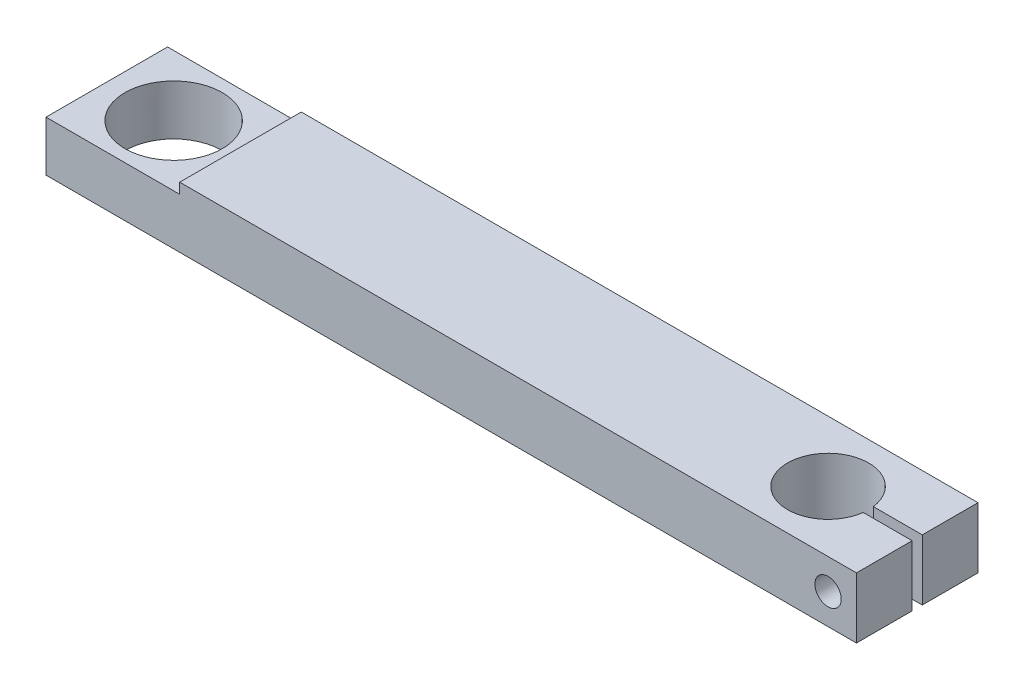
SolidWorks part; units mm, degrees
material "1060 Alloy"
ref_plane "Front Plane" through (0, 0, 0) normal (0, 0, 1) x (1, 0, 0)
ref_plane "Top Plane" through (0, 0, 0) normal (0, 1, 0) x (1, 0, 0)
ref_plane "Right Plane" through (0, 0, 0) normal (1, 0, 0) x (0, 0, -1)
sketch "Sketch1" plane through (0, 0, 0) normal (0, 1, 0) x (1, 0, 0)
  line L0 (87.9216, 1.25) -> (100, 1.25)
  line L1 (-100, 15) -> (100, 15)
  line L2 (-100, 15) -> (-100, -15)
  line L3 (-100, -15) -> (100, -15)
  line L4 (100, 15) -> (100, -15)
  line L5 (-100, 15) -> (100, -15) construction
  line L6 (-100, -15) -> (100, 15) construction
  line L7 (100, 1.25) -> (100, 0)
  line L8 (100, 0) -> (100, -1.25)
  line L9 (100, -1.25) -> (87.9216, -1.25)
  line L10 (78, 0) -> (119.9391, 0) construction
  circle A0 centre (-83.5, 0) radius 12
  circle A1 centre (78, 0) radius 10
  point P0 (0, 0)
  dimension "D3" = 24
  dimension "D4" = 20
  dimension "D1" = 200
  dimension "D2" = 30
  dimension "D5" = 16.5
  dimension "D6" = 161.5
  dimension "D7" = 2.5
  dimension "D8" = 1.25
extrude "Boss-Extrude1" add sketch "Sketch1" along normal blind 15 contours A1 L0 L4 L1 L2 L3 L9 A0
sketch "Sketch2" plane through (0, 0, -15) normal (0, 0, -1) x (-1, 0, 0)
  line L0 (100, 0) -> (-100, 0) construction
  line L1 (-100, 15) -> (-100, 0) construction
  circle A0 centre (-93, 7.5) radius 5.25
  dimension "D1" = 10.5
  dimension "D2" = 7.5
  dimension "D3" = 7
extrude "Cut-Extrude1" cut sketch "Sketch2" against normal blind 7
sketch "Sketch3" plane through (0, 0, -8) normal (0, 0, -1) x (-1, 0, 0)
  circle A0 centre (-93, 7.5) radius 3.25
  dimension "D1" = 6.5
extrude "Cut-Extrude2" cut sketch "Sketch3" against normal through all
sketch "Sketch4" plane through (0, 0, -15) normal (0, 0, -1) x (-1, 0, 0)
  line L0 (100, 12.4) -> (67, 12.4)
  line L1 (100, 15) -> (100, 0) construction
  line L2 (67, 12.4) -> (67, 15)
  line L3 (100, 15) -> (-100, 15) construction
  line L4 (67, 15) -> (100, 15)
  line L5 (100, 15) -> (100, 12.4)
  dimension "D1" = 2.6
  dimension "D2" = 33
extrude "Cut-Extrude3" cut sketch "Sketch4" against normal through all
